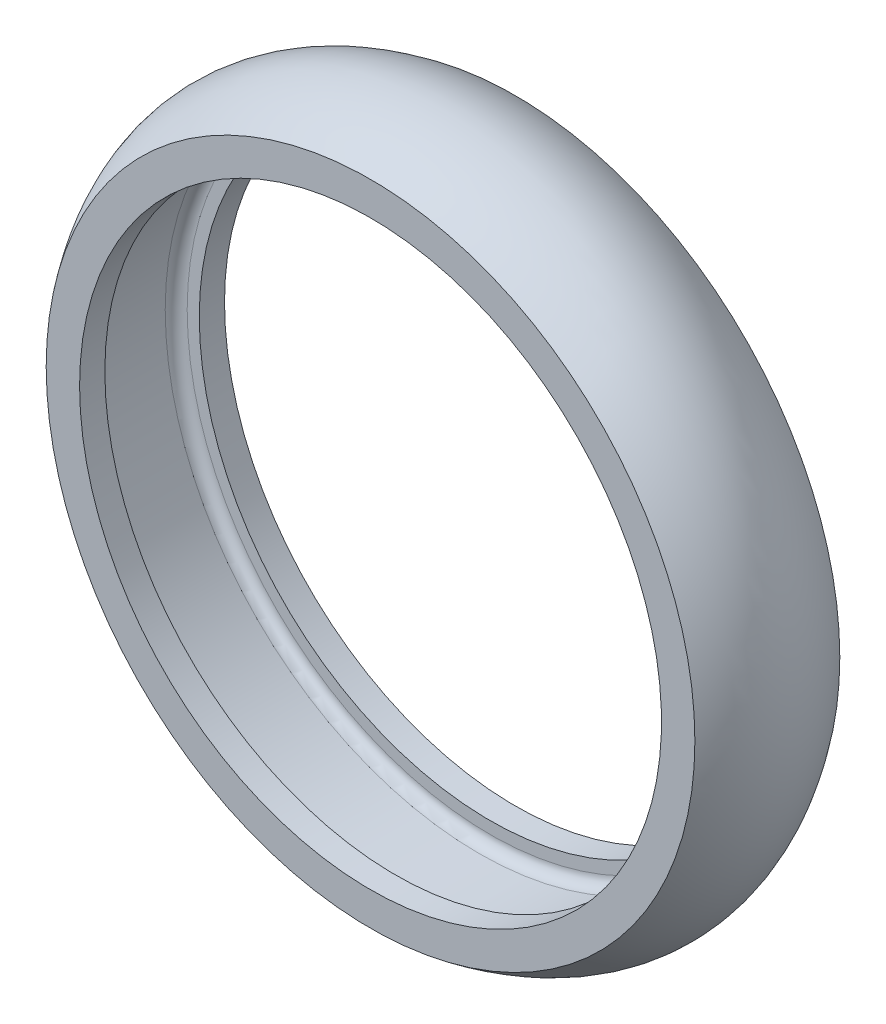
SolidWorks part; units mm, degrees
ref_plane "Alzado" through (0, 0, 0) normal (0, 0, 1) x (1, 0, 0)
ref_plane "Planta" through (0, 0, 0) normal (0, 1, 0) x (1, 0, 0)
ref_plane "Vista lateral" through (0, 0, 0) normal (1, 0, 0) x (0, 0, -1)
sketch "Croquis1" plane through (0, 0, 0) normal (0, 1, 0) x (1, 0, 0)
  line L0 (0, 0) -> (14.3, 0) construction
  line L1 (14.3, 0) -> (14.3, 3.3) construction
  line L2 (14.3, 0) -> (14.3, -3.3) construction
  line L3 (14.3, 1.65) -> (14.3, -1.65)
  line L4 (0, 0) -> (16, 0) construction
  line L5 (14.3, 3.3) -> (14.7708, 3.3)
  line L6 (0, 4.6214) -> (0, -3.9581) construction
  line L7 (14.7708, -3.3) -> (14.3, -3.3)
  line L8 (14.3, 3.3) -> (13.25, 3.3)
  line L9 (14.3, -3.3) -> (13.25, -3.3)
  line L10 (13.25, -3.3) -> (13.25, -2.15)
  line L11 (13.25, 3.3) -> (13.25, 2.15)
  line L12 (13.25, 2.15) -> (13.8, 2.15)
  line L13 (13.25, -2.15) -> (13.8, -2.15)
  arc A0 (14.3, -1.65) -> (13.8, -2.15) centre (13.8, -1.65) cw
  arc A1 (14.3, 1.65) -> (13.8, 2.15) centre (13.8, 1.65) ccw
  spline S0 degree 2 poles (14.7708, 3.3) (17.2292, 0) (14.7708, -3.3) knots 0 0 0 1 1 1
  dimension "D1" = 0.5
revolve "Revolución1" add sketch "Croquis1" angle 360 about L6
